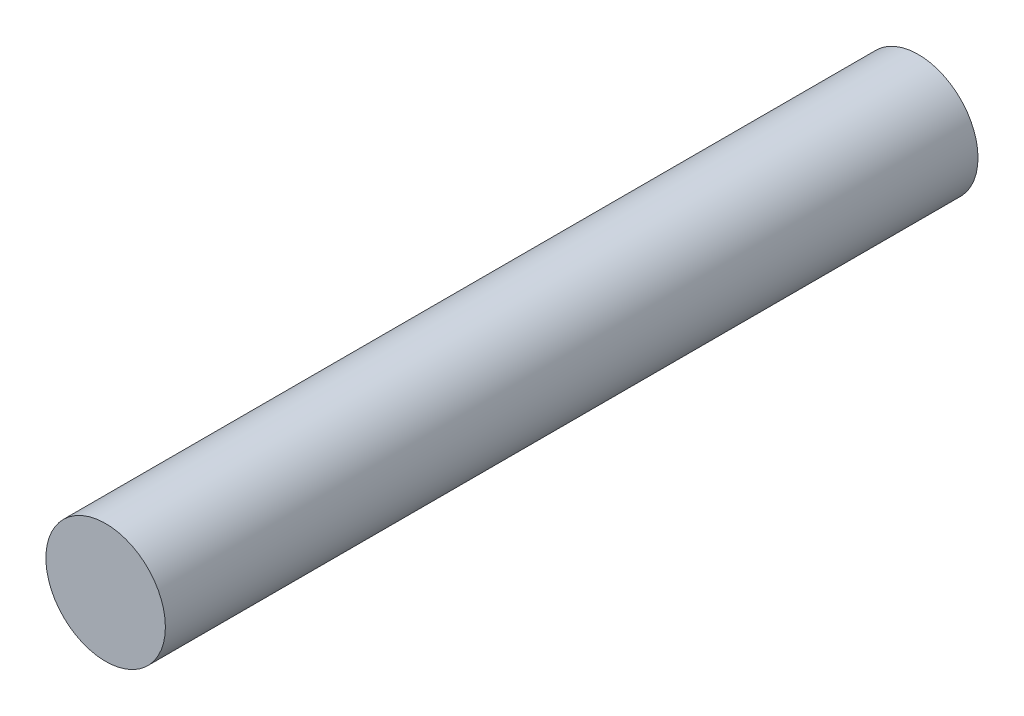
SolidWorks part; units mm, degrees
material "ABS"
ref_plane "Front Plane" through (0, 0, 0) normal (0, 0, 1) x (1, 0, 0)
ref_plane "Top Plane" through (0, 0, 0) normal (0, 1, 0) x (1, 0, 0)
ref_plane "Right Plane" through (0, 0, 0) normal (1, 0, 0) x (0, 0, -1)
sketch "Sketch1" plane through (0, 0, 0) normal (0, 0, 1) x (1, 0, 0)
  circle A0 centre (0, 0) radius 1.25
  dimension "D1" = 2.5
extrude "Boss-Extrude1" add sketch "Sketch1" along normal blind 17
